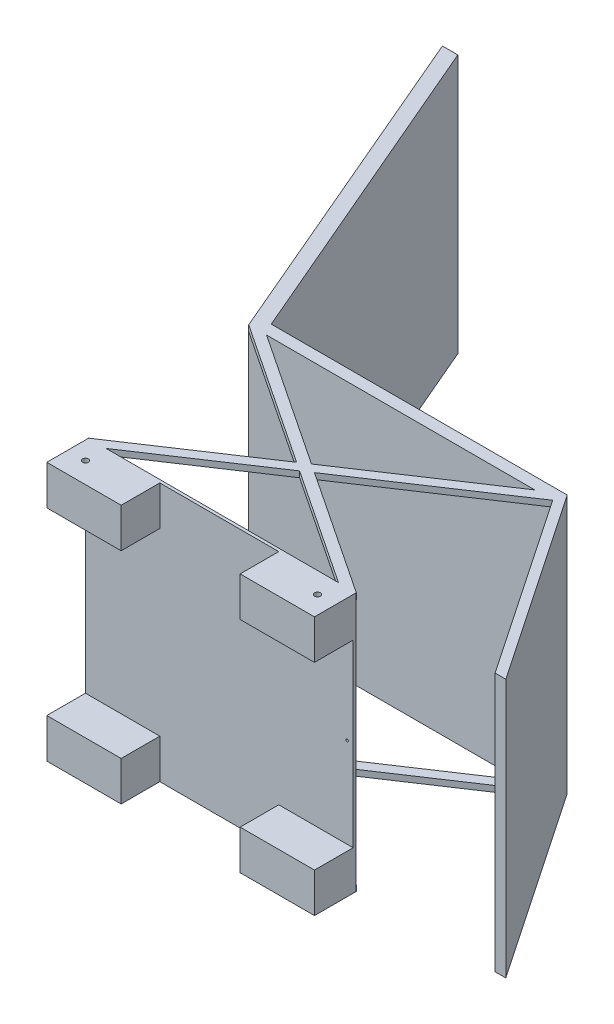
SolidWorks part; units mm, degrees
ref_plane "前视基准面" through (0, 0, 0) normal (0, 0, 1) x (1, 0, 0)
ref_plane "上视基准面" through (0, 0, 0) normal (0, 1, 0) x (1, 0, 0)
ref_plane "右视基准面" through (0, 0, 0) normal (1, 0, 0) x (0, 0, -1)
sketch "草图1" plane through (0, 0, 0) normal (0, 0, 1) x (1, 0, 0)
  line L0 (195, 0) -> (-195, 0) construction
  line L1 (0, 237.5) -> (0, -237.5) construction
  line L2 (195, 0) -> (195, 237.5) construction
  line L3 (195, 237.5) -> (-195, 237.5) construction
  line L4 (-195, 237.5) -> (-195, -237.5) construction
  line L5 (-195, -237.5) -> (195, -237.5) construction
  line L6 (195, -237.5) -> (195, 0) construction
  line L7 (195, 0) -> (225, 0) construction
  line L8 (225, 0) -> (225, 217.5)
  line L9 (225, 217.5) -> (-225, 217.5)
  line L10 (-225, 217.5) -> (-225, 0)
  line L11 (-225, 0) -> (-225, -217.5)
  line L12 (-225, -217.5) -> (225, -217.5)
  line L13 (225, -217.5) -> (225, 0)
  point P4 (0, 0)
  point P8 (0, 0)
  dimension "D1" = 30
  dimension "D2" = 217.5
  dimension "D3" = 450
  dimension "D4" = 217.5
extrude "凸台-拉伸1" add sketch "草图1" along normal blind 70
sketch "草图2" plane through (0, 0, 70) normal (0, 0, 1) x (1, 0, 0)
  line L0 (0, -151.164) -> (0, 151.164) construction
  line L1 (0, 217.5) -> (-100, 217.5) construction
  line L2 (225, 217.5) -> (-225, 217.5) construction
  line L3 (-100, 217.5) -> (-100, 151.164)
  line L4 (-100, 151.164) -> (-225, 151.164)
  line L5 (-225, 217.5) -> (-225, -217.5) construction
  line L6 (-225, 151.164) -> (-225, -151.164)
  line L7 (-225, 0) -> (225, 0) construction
  line L8 (225, -217.5) -> (225, 217.5) construction
  line L9 (-100, -217.5) -> (-100, -151.164)
  line L10 (-100, -151.164) -> (-225, -151.164)
  line L11 (100, 217.5) -> (100, 151.164)
  line L12 (100, 151.164) -> (225, 151.164)
  line L13 (100, -151.164) -> (225, -151.164)
  line L14 (100, -217.5) -> (100, -151.164)
  line L15 (225, 151.164) -> (225, -151.164)
  line L16 (0, 217.5) -> (100, 217.5)
  line L17 (-100, -217.5) -> (100, -217.5)
  point P4 (0, 0)
  dimension "D1" = 100
extrude "切除-拉伸1" cut sketch "草图2" against normal blind 65 and the other way through all
sketch "草图3" plane through (0, 217.5, 0) normal (0, 1, 0) x (1, 0, 0)
  line L0 (-225, 0) -> (-195, 0) construction
  line L1 (225, 0) -> (-225, 0) construction
  line L2 (-195, 0) -> (-195, -70) construction
  line L3 (-100, -70) -> (-225, -70) construction
  line L4 (0, 0) -> (0, -117.5368) construction
  line L5 (195, 0) -> (195, -70) construction
  line L6 (225, 0) -> (195, 0) construction
  circle A0 centre (-195, -35) radius 5
  circle A1 centre (195, -35) radius 5
  dimension "D2" = 10
  dimension "D1" = 30
sketch "草图4" plane through (0, 0, 5) normal (0, 0, 1) x (1, 0, 0)
  line L0 (225, 0) -> (215, 0) construction
  line L1 (225, -151.164) -> (225, 151.164) construction
  circle A0 centre (215, 0) radius 2
  dimension "D2" = 4
  dimension "D1" = 10
extrude "切除-拉伸2" cut sketch "草图4" against normal blind 10
extrude "切除-拉伸3" cut sketch "草图3" against normal blind 10
mirror "镜向1" about plane through (0, 0, 0) normal (0, 1, 0) of "切除-拉伸3"
sketch "草图6" plane through (0, -217.5, 0) normal (0, -1, 0) x (-1, 0, 0)
  line L1 (-225.4733, 0) -> (-15.0316, 140)
  line L3 (0, 130) -> (-195.4102, 0)
  line L4 (225, 0) -> (-225, 0) construction
  line L5 (-195.4102, 0) -> (-225.4733, 0)
  line L6 (0, 130) -> (195.4102, 0)
  line L7 (225.4733, 0) -> (15.0316, 140)
  line L8 (195.4102, 0) -> (225.4733, 0)
  line L10 (-195.4102, 0) -> (-225.4733, 0)
  line L11 (-225.4733, 0) -> (-15.0316, 140)
  line L12 (0, 130) -> (-195.4102, 0)
  line L13 (195.4102, 0) -> (225.4733, 0)
  line L14 (0, 130) -> (195.4102, 0)
  line L15 (225.4733, 0) -> (15.0316, 140)
  line L16 (15.0316, 140) -> (255.5364, 300)
  line L17 (0, 150) -> (225.4733, 300)
  line L18 (225.4733, 300) -> (255.5364, 300)
  line L19 (-225.4733, 300) -> (-255.5364, 300)
  line L20 (0, 150) -> (-225.4733, 300)
  line L21 (-15.0316, 140) -> (-255.5364, 300)
  line M15 (225, 0) -> (-225, 0)
extrude "凸台-拉伸2" add sketch "草图6" against normal blind 10 contours L21 L1 L5 L3 L6 L8 L7 L16 L18 L17 L20 L19 M15
mirror "镜向2" about plane through (0, 0, 0) normal (0, 1, 0) of "凸台-拉伸2"
sketch "草图7" plane through (0, 217.5, 0) normal (0, 1, 0) x (1, 0, 0)
  line L0 (-255.5364, 300) -> (255.5364, 300)
  line L1 (255.5364, 300) -> (458.6756, 0)
  line L2 (458.6756, 0) -> (476.6394, 0)
  line L3 (476.6394, 0) -> (260.0732, 319.8293)
  line L8 (-255.5364, 300) -> (-498.5368, 868.6716)
  line L9 (260.0732, 319.8293) -> (-237.4901, 319.8293)
  line L10 (-237.4901, 319.8293) -> (-472.6601, 868.6716)
  line L11 (-472.6601, 868.6716) -> (-498.5368, 868.6716)
extrude "凸台-拉伸3" add sketch "草图7" against normal blind 435
